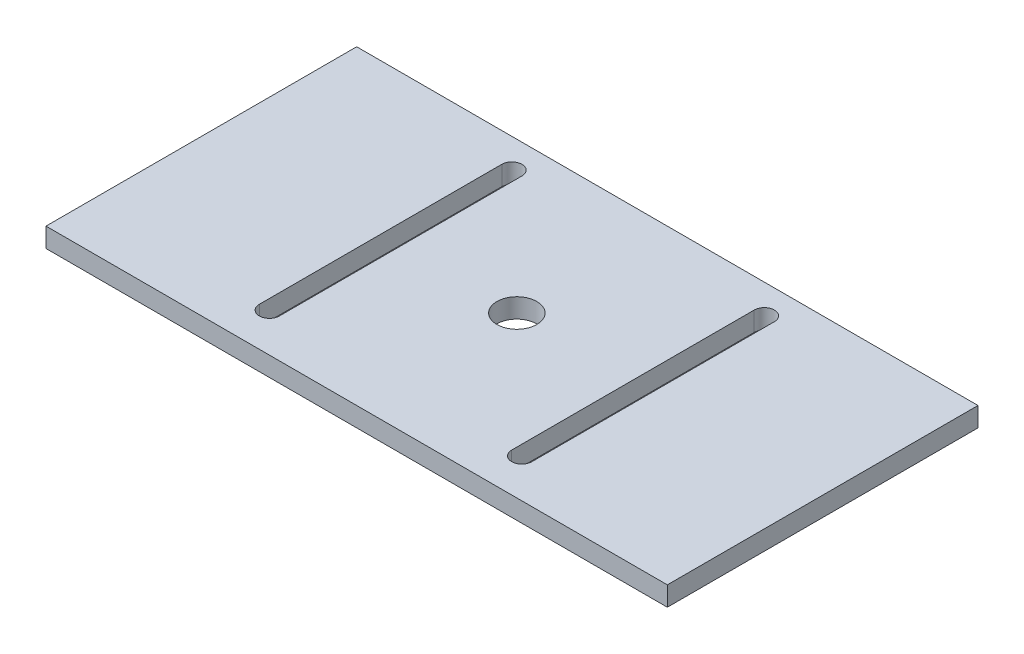
SolidWorks part; units mm, degrees
ref_plane "Front Plane" through (0, 0, 0) normal (0, 0, 1) x (1, 0, 0)
ref_plane "Top Plane" through (0, 0, 0) normal (0, 1, 0) x (1, 0, 0)
ref_plane "Right Plane" through (0, 0, 0) normal (1, 0, 0) x (0, 0, -1)
sketch "Sketch2" plane through (0, 0, 0) normal (0, 1, 0) x (1, 0, 0)
  line L0 (50.8, 0) -> (50.8, 50.8) construction
  line L1 (0, 0) -> (101.6, 0)
  line L2 (0, 0) -> (0, 50.8)
  line L3 (0, 50.8) -> (101.6, 50.8)
  line L4 (101.6, 0) -> (101.6, 50.8)
  line L5 (50.8, 26.1913) -> (30.1625, 26.1913) construction
  line L6 (30.1625, 6.364) -> (30.1625, 46.0186) construction
  line L7 (28.5115, 6.364) -> (28.5115, 46.0186)
  line L8 (31.8135, 6.364) -> (31.8135, 46.0186)
  line L9 (71.4375, 6.364) -> (71.4375, 46.0186) construction
  line L10 (73.0885, 6.364) -> (73.0885, 46.0186)
  line L11 (69.7865, 6.364) -> (69.7865, 46.0186)
  arc A0 (28.5115, 6.364) -> (31.8135, 6.364) centre (30.1625, 6.364) ccw
  arc A1 (31.8135, 46.0186) -> (28.5115, 46.0186) centre (30.1625, 46.0186) ccw
  arc A2 (73.0885, 6.364) -> (69.7865, 6.364) centre (71.4375, 6.364) cw
  arc A3 (69.7865, 46.0186) -> (73.0885, 46.0186) centre (71.4375, 46.0186) cw
  circle A4 centre (50.8, 26.1913) radius 3.2639
  point P11 (30.1625, 26.1913)
  point P18 (71.4375, 26.1913)
  dimension "D5" = 6.5278
  dimension "D1" = 101.6
  dimension "D2" = 50.8
  dimension "D3" = 20.6375
  dimension "D4" = 3.302
extrude "Boss-Extrude1" add sketch "Sketch2" along normal blind 3.175
